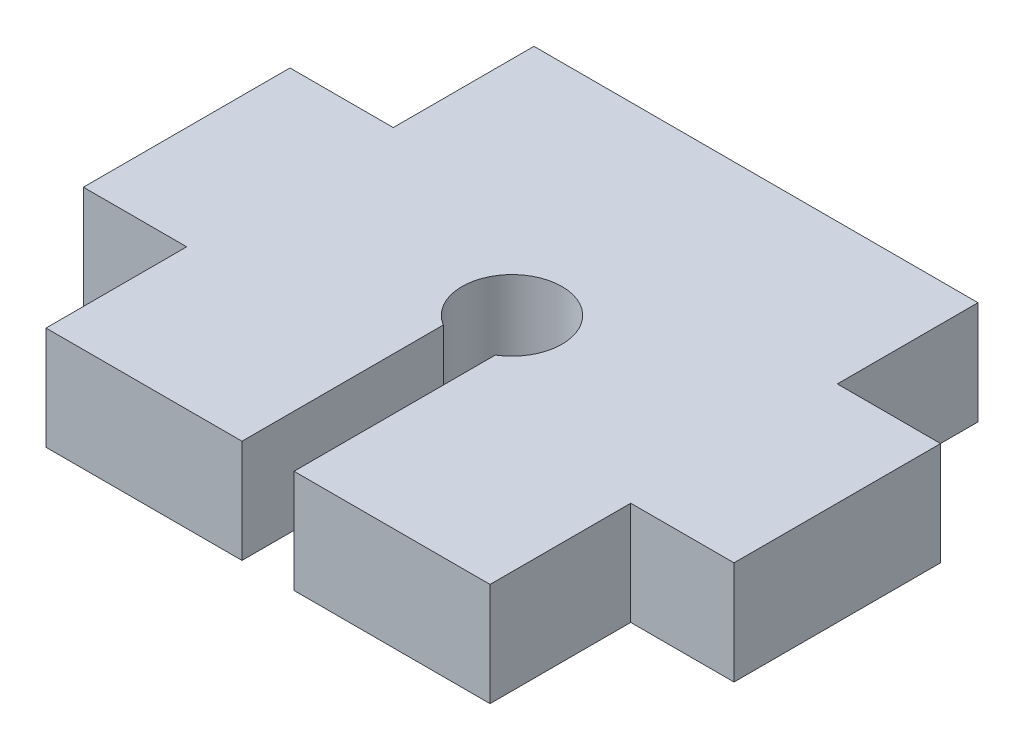
SolidWorks part; units mm, degrees
material "Acrylic (Medium-high impact)"
ref_plane "Front Plane" through (0, 0, 0) normal (0, 0, 1) x (1, 0, 0)
ref_plane "Top Plane" through (0, 0, 0) normal (0, 1, 0) x (1, 0, 0)
ref_plane "Right Plane" through (0, 0, 0) normal (1, 0, 0) x (0, 0, -1)
sketch "Sketch2" plane through (0, 0, 0) normal (0, 1, 0) x (1, 0, 0)
  line L1 (-13.65, -15) -> (13.65, -15)
  line L2 (-13.65, -15) -> (-13.65, 15)
  line L3 (-13.65, 15) -> (13.65, 15)
  line L4 (13.65, -15) -> (13.65, 15)
  line L5 (-13.65, -15) -> (13.65, 15) construction
  line L6 (-13.65, 15) -> (13.65, -15) construction
  point P0 (0, 0)
  dimension "D1" = 27.3
  dimension "D2" = 30
extrude "Boss-Extrude1" add sketch "Sketch2" along normal blind 6.35
sketch "Sketch3" plane through (13.65, 0, 0) normal (1, 0, 0) x (0, 0, -1)
  line L0 (15, 6.35) -> (-15, 6.35) construction
  line L1 (6.35, 0) -> (-6.35, 0)
  line L2 (6.35, 0) -> (6.35, 6.35)
  line L3 (6.35, 6.35) -> (-6.35, 6.35)
  line L4 (-6.35, 0) -> (-6.35, 6.35)
  line L5 (6.35, 0) -> (-6.35, 6.35) construction
  line L6 (6.35, 6.35) -> (-6.35, 0) construction
  line L7 (15, 0) -> (-15, 0) construction
  line L8 (15, 6.35) -> (15, 0) construction
  point P0 (0, 3.175)
  dimension "D1" = 0
  dimension "D2" = 0
  dimension "D3" = 12.7
  dimension "D4" = 15
extrude "Boss-Extrude2" add sketch "Sketch3" along normal blind 6.35
mirror "Mirror1" about plane through (0, 0, 0) normal (1, 0, 0) of "Boss-Extrude2"
ref_point "Point1"
sketch "Sketch4" plane through (0, 6.35, 0) normal (0, 1, 0) x (1, 0, 0)
  circle A0 centre (0, 0) radius 3.075
  dimension "D1" = 6.15
extrude "Cut-Extrude1" cut sketch "Sketch4" against normal through all
sketch "Sketch5" plane through (0, 0, 15) normal (0, 0, 1) x (1, 0, 0)
  line L0 (-13.65, 6.35) -> (13.65, 6.35) construction
  line L1 (-1.6, 0) -> (1.6, 0)
  line L2 (-1.6, 0) -> (-1.6, 6.35)
  line L3 (-1.6, 6.35) -> (1.6, 6.35)
  line L4 (1.6, 0) -> (1.6, 6.35)
  line L5 (-1.6, 0) -> (1.6, 6.35) construction
  line L6 (-1.6, 6.35) -> (1.6, 0) construction
  line L7 (-13.65, 0) -> (13.65, 0) construction
  line L8 (-13.65, 6.35) -> (-13.65, 0) construction
  point P0 (0, 3.175)
  dimension "D1" = 0
  dimension "D2" = 0
  dimension "D3" = 13.65
  dimension "D4" = 3.2
extrude "Cut-Extrude2" cut sketch "Sketch5" against normal up to next
